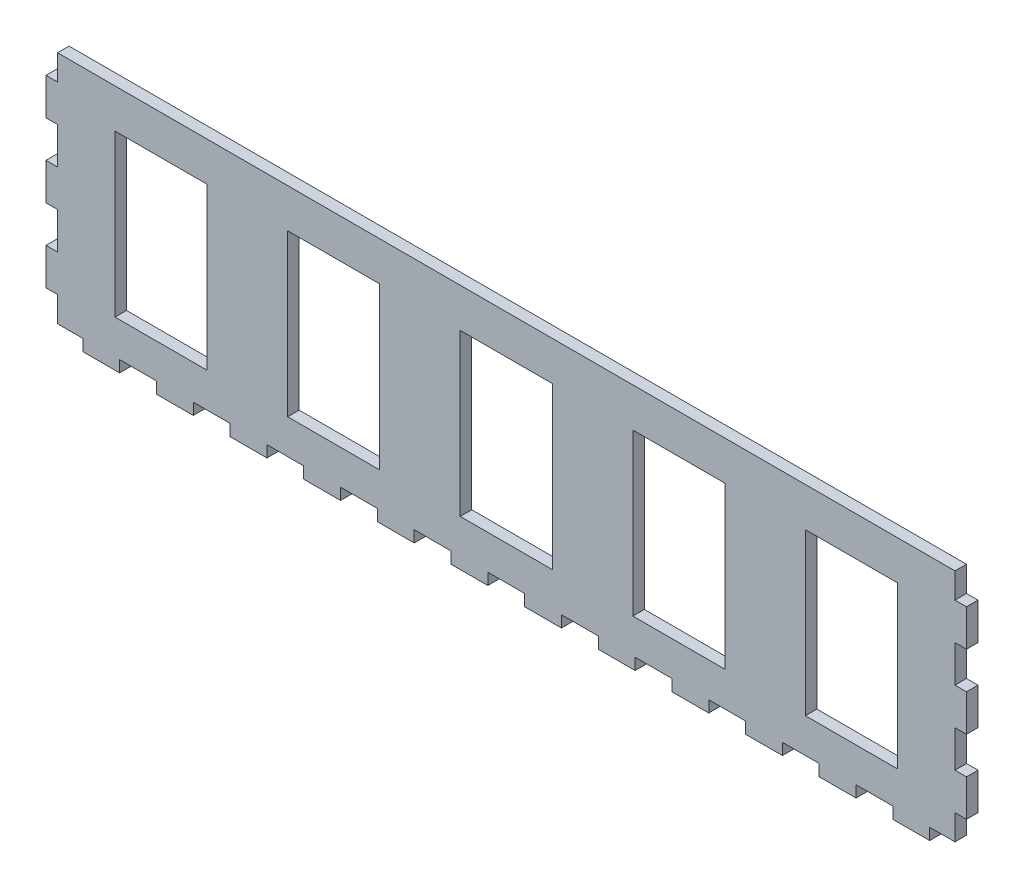
SolidWorks part; units mm, degrees
ref_plane "Plan de face" through (0, 0, 0) normal (0, 0, 1) x (1, 0, 0)
ref_plane "Plan de dessus" through (0, 0, 0) normal (0, 1, 0) x (1, 0, 0)
ref_plane "Plan de droite" through (0, 0, 0) normal (1, 0, 0) x (0, 0, -1)
sketch "Esquisse1" plane through (0, 0, 0) normal (0, 0, 1) x (1, 0, 0)
  line L1 (0, 0) -> (400, 0)
  line L2 (0, 0) -> (0, -107)
  line L3 (0, -107) -> (400, -107)
  line L4 (400, 0) -> (400, -107)
  dimension "D1" = 400
  dimension "D2" = 107
extrude "Boss.-Extru.1" add sketch "Esquisse1" along normal blind 5
sketch "Esquisse2" plane through (0, 0, 5) normal (0, 0, 1) x (1, 0, 0)
  line L0 (0, 0) -> (400, 0) construction
  line L1 (0, -107) -> (5, -107)
  line L2 (0, -107) -> (0, -91)
  line L3 (0, -91) -> (5, -91)
  line L4 (5, -107) -> (5, -91)
  dimension "D1" = 16
  dimension "D2" = 400
  dimension "D3" = 5
extrude "Enlèv. mat.-Extru.1" cut sketch "Esquisse2" against normal blind 5
pattern_linear "Répétition linéaire1" count 4 spacing 32 along (0, 1, 0) of "Enlèv. mat.-Extru.1"
ref_plane "Plan1" through (200, 0, 0) normal (-1, 0, 0) x (0, 0, 1)
mirror "Symétrie1" about plane through (200, 0, 0) normal (-1, 0, 0) of "Répétition linéaire1", "Enlèv. mat.-Extru.1"
sketch "Esquisse3" plane through (0, 0, 5) normal (0, 0, 1) x (1, 0, 0)
  line L0 (0, -75) -> (0, -91) construction
  line L1 (0, -107) -> (16, -107)
  line L2 (0, -107) -> (0, -102)
  line L3 (0, -102) -> (16, -102)
  line L4 (16, -107) -> (16, -102)
  line L5 (5, -107) -> (395, -107) construction
  line L6 (0, -18.7177) -> (400, -18.7177) construction
  line L7 (0, -11) -> (0, -27) construction
  line L8 (400, -27) -> (400, -11) construction
  point P14 (8, -107)
  dimension "D3" = 5
  dimension "D1" = 400
  dimension "D2" = 16
extrude "Enlèv. mat.-Extru.2" cut sketch "Esquisse3" against normal blind 5
pattern_linear "Répétition linéaire2" count 13 spacing 32 along (1, 0, 0) of "Enlèv. mat.-Extru.2"
sketch "Esquisse4" plane through (0, 0, 5) normal (0, 0, 1) x (1, 0, 0)
  line L0 (48, -107) -> (64, -107) construction
  line L1 (30, -17) -> (70, -17)
  line L2 (30, -17) -> (30, -87)
  line L3 (30, -87) -> (70, -87)
  line L4 (70, -17) -> (70, -87)
  line L5 (0, -43) -> (0, -59) construction
  dimension "D1" = 40
  dimension "D2" = 70
  dimension "D3" = 20
  dimension "D4" = 30
extrude "Enlèv. mat.-Extru.3" cut sketch "Esquisse4" against normal blind 10
pattern_linear "Répétition linéaire3" count 5 spacing 75 along (1, 0, 0) of "Enlèv. mat.-Extru.3"
equation "\"D1@Esquisse2\"=\"D2@Esquisse2\"/25"
equation "\"D2@Esquisse3\"=\"D1@Esquisse3\"/25"
equation "\"D2@Esquisse1\"=110.00mm-3"
